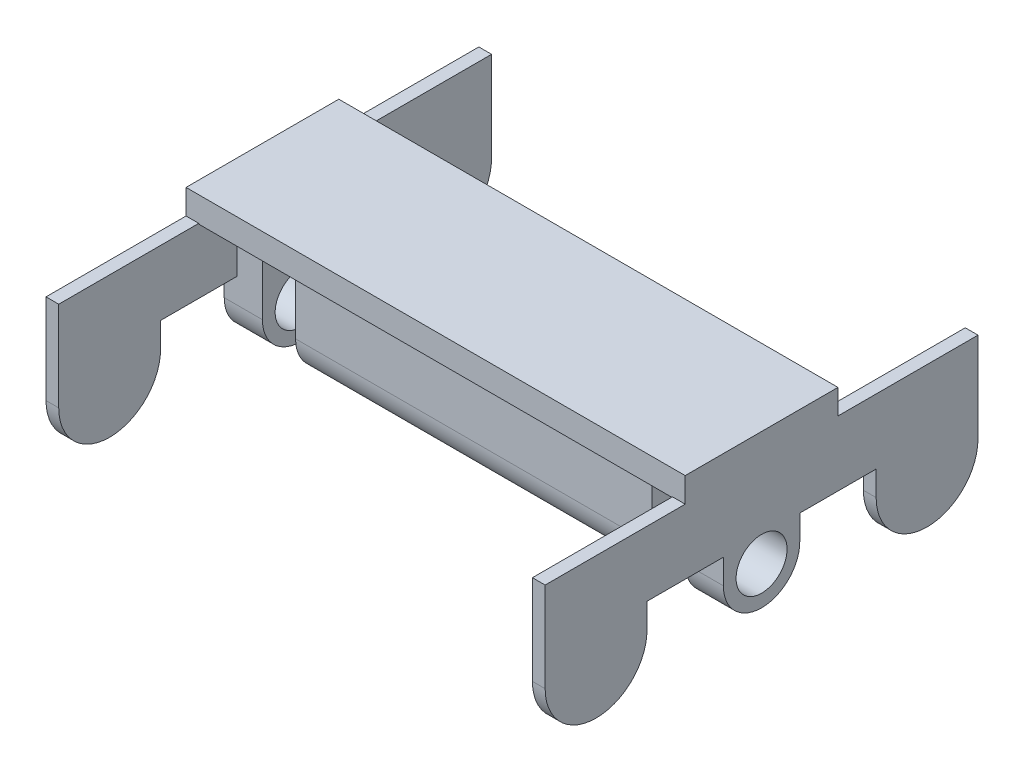
SolidWorks part; units mm, degrees
ref_plane "Front Plane" through (0, 0, 0) normal (0, 0, 1) x (1, 0, 0)
ref_plane "Top Plane" through (0, 0, 0) normal (0, 1, 0) x (1, 0, 0)
ref_plane "Right Plane" through (0, 0, 0) normal (1, 0, 0) x (0, 0, -1)
sketch "Sketch1" plane through (0, 0, 0) normal (1, 0, 0) x (0, 0, -1)
  line L0 (0, -0.5) -> (0, -4) construction
  line L1 (3, -0.5) -> (-3, -0.5)
  line L2 (3, -0.5) -> (3, 0.5)
  line L3 (3, 0.5) -> (-3, 0.5)
  line L4 (-3, -0.5) -> (-3, 0.5)
  line L5 (3, -0.5) -> (-3, 0.5) construction
  line L6 (3, 0.5) -> (-3, -0.5) construction
  line L7 (-1.5, -4) -> (-1.5, -0.5)
  line L8 (1.5, -4) -> (1.5, -0.5)
  circle A0 centre (0, -4) radius 1.001
  arc A1 (-1.5, -4) -> (1.5, -4) centre (0, -4) ccw
  point P0 (0, 0)
  dimension "D3" = 2.002
  dimension "D4" = 1.5
  dimension "D1" = 6
  dimension "D2" = 1
extrude "Boss-Extrude1" add sketch "Sketch1" along normal blind 18.604 contours L7 A1 L8 L1 A0 | L4 L1 L2 L3
sketch "Sketch2" plane through (0, 0, 3) normal (0, 0, 1) x (1, 0, 0)
  line L0 (9.302, 0.5) -> (9.302, -6.8964) construction
  line L2 (9.302, -1.4097) -> (1, -1.4097) construction
  line L3 (9.302, -2.3475) -> (16.302, -2.3475) construction
  line L4 (9.302, -2.3475) -> (2.302, -2.3475) construction
  line L5 (9.302, -1.4097) -> (17.604, -1.4097) construction
  line L6 (1, -0.5) -> (2.302, -0.5)
  line L7 (1, -0.5) -> (1, -6.3043)
  line L8 (2.302, -0.5) -> (2.302, -6.3043)
  line L9 (1, -6.3043) -> (2.302, -6.3043)
  line L10 (18.604, -0.5) -> (0, -0.5) construction
  line L11 (17.604, -0.5) -> (16.302, -0.5)
  line L12 (17.604, -0.5) -> (17.604, -6.4096)
  line L13 (16.302, -0.5) -> (16.302, -6.4096)
  line L14 (17.604, -6.4096) -> (16.302, -6.4096)
extrude "Cut-Extrude1" cut sketch "Sketch2" against normal up to next
sketch "Sketch3" plane through (2.302, 0, 0) normal (-1, 0, 0) x (0, 0, 1)
  line L0 (0, -2.999) -> (1.5, -2.999) construction
  line L1 (1.5, -4) -> (1.5, -0.5) construction
  line L2 (1.2532, -0.5) -> (1.2532, -2.999) construction
  circle A0 centre (0, -4) radius 1.001 construction
  circle A1 centre (0, -1.75) radius 0.75
  dimension "D1" = 1.5
extrude "Cut-Extrude2" cut sketch "Sketch3" against normal up to next
sketch "Sketch4" plane through (18.604, 0, 0) normal (1, 0, 0) x (0, 0, -1)
  line L0 (1.5, -0.9089) -> (8.5, -0.9089) construction
  line L1 (1.5, -4) -> (1.5, -0.5) construction
  line L2 (1.5, -1.4832) -> (4.5, -1.4832) construction
  line L3 (0, -0.5) -> (0, -2.999) construction
  line L4 (-4.5, -3.0263) -> (-1.5, -3.0263)
  line L5 (-8.5, -3.0263) -> (-8.5, -0.4727)
  line L6 (8.5, -3.0263) -> (8.5, -0.4727)
  line L7 (-8.5, -0.4727) -> (-3, -0.4727)
  line L8 (-8.5, -3.0263) -> (8.5, -0.4727) construction
  line L9 (8.5, -3.0263) -> (-8.5, -0.4727) construction
  line L10 (-1.5, -4) -> (-1.5, -3.0263)
  line L11 (1.5, -4) -> (1.5, -3.0263)
  line L12 (4.5, -4) -> (4.5, -3.0263)
  line L13 (8.5, -4) -> (8.5, -3.0263)
  line L14 (-8.5, -4) -> (-8.5, -3.0263)
  line L15 (-4.5, -4) -> (-4.5, -3.0263)
  line L16 (3, -0.4727) -> (8.5, -0.4727)
  line L17 (-3, 0.5) -> (3, 0.5)
  line L18 (-3, 0.5) -> (-3, -0.5)
  line L19 (-0.232, -3.0263) -> (0.232, -3.0263)
  line L20 (3, 0.5) -> (3, -0.5)
  line L21 (1.5, -3.0263) -> (4.5, -3.0263)
  circle A0 centre (0, -4) radius 1.001 construction
  arc A1 (-1.5, -4) -> (1.5, -4) centre (0, -4) ccw
  arc A2 (-1.5, -4) -> (1.5, -4) centre (0, -4) ccw construction
  arc A3 (8.5, -4) -> (4.5, -4) centre (6.5, -4) cw
  arc A4 (-8.5, -4) -> (-4.5, -4) centre (-6.5, -4) ccw
  circle A5 centre (0, -4) radius 1.001
  point P12 (0, -1.7495)
extrude "Boss-Extrude2" add sketch "Sketch4" along normal blind 0.5
ref_plane "Plane1" through (9.302, 0, 0) normal (-1, 0, 0) x (0, 0, 1)
mirror "Mirror2" about plane through (9.302, 0, 0) normal (-1, 0, 0) of "Boss-Extrude2"
